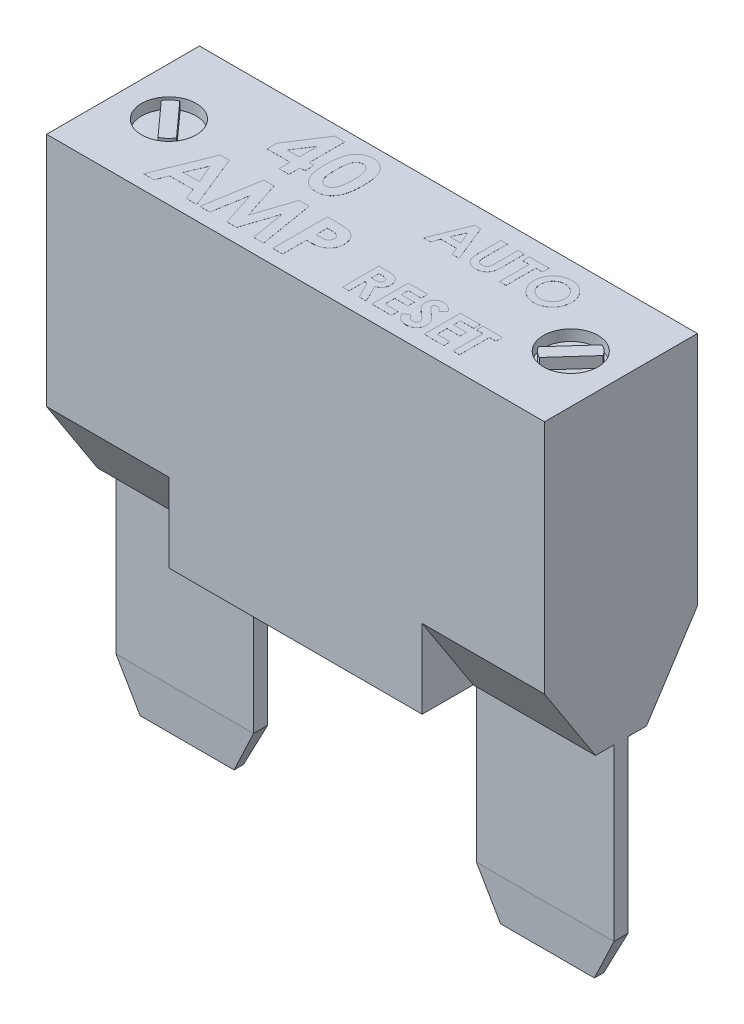
SolidWorks part; units mm, degrees
material "Free-Cutting Brass, UNS C36000"
ref_plane "Front Plane" through (0, 0, 0) normal (0, 0, 1) x (1, 0, 0)
ref_plane "Top Plane" through (0, 0, 0) normal (0, 1, 0) x (1, 0, 0)
ref_plane "Right Plane" through (0, 0, 0) normal (1, 0, 0) x (0, 0, -1)
sketch "Sketch1" plane through (0, 0, 0) normal (1, 0, 0) x (0, 0, -1)
  line L0 (-4.445, 4.572) -> (-1.4816, 0)
  line L1 (-1.4816, 0) -> (1.4816, 0)
  line L2 (0, 0) -> (0, 18.288) construction
  line L6 (1.4816, 0) -> (4.445, 4.572)
  line L7 (4.445, 4.572) -> (4.445, 18.288)
  line L8 (4.445, 18.288) -> (-4.445, 18.288)
  line L9 (-4.445, 18.288) -> (-4.445, 4.572)
  dimension "D1" = 8.89
  dimension "D2" = 18.288
  dimension "D3" = 32.95
  dimension "D4" = 4.572
extrude "Extrude1" add sketch "Sketch1" along normal mid plane 28.956
sketch "Sketch2" plane through (0, 0, 0) normal (1, 0, 0) x (0, 0, -1)
  line L0 (4.445, 18.288) -> (-4.445, 18.288) construction
  line L1 (-4.445, 0) -> (4.445, 0)
  line L2 (-4.445, 0) -> (-4.445, 18.288)
  line L3 (-4.445, 18.288) -> (4.445, 18.288)
  line L4 (4.445, 0) -> (4.445, 18.288)
  line L5 (4.445, 4.572) -> (4.445, 18.288) construction
  line L6 (-1.4816, 0) -> (1.4816, 0) construction
  line L7 (-4.445, 18.288) -> (-4.445, 4.572) construction
extrude "Extrude2" add sketch "Sketch2" along normal mid plane 14.732
sketch "Sketch3" plane through (0, 0, 0) normal (0, -1, 0) x (1, 0, 0)
  line L0 (-14.478, 1.4816) -> (-14.478, -1.4816) construction
  line L1 (-14.478, 0.4064) -> (-6.477, 0.4064)
  line L2 (-14.478, 0.4064) -> (-14.478, -0.4064)
  line L3 (-14.478, -0.4064) -> (-6.477, -0.4064)
  line L4 (-6.477, 0.4064) -> (-6.477, -0.4064)
  line L5 (-14.478, 0.4064) -> (-6.477, -0.4064) construction
  line L6 (-14.478, -0.4064) -> (-6.477, 0.4064) construction
  line L7 (0, 0) -> (-14.478, 0) construction
  point P0 (-10.4775, 0)
  dimension "D1" = 8.001
  dimension "D2" = 0.8128
extrude "Extrude3" add sketch "Sketch3" along normal blind 12.446
chamfer "Chamfer1" distance 2.54 angle 3 2 edges at (-10.4775, -12.446, -0.4064) (-10.4775, -12.446, 0.4064)
chamfer "Chamfer2" distance 2.54 angle 26.57 2 edges at (-14.478, -12.446, 0) (-6.477, -12.446, 0)
sketch "Sketch4" plane through (0, 18.288, 0) normal (0, 1, 0) x (1, 0, 0)
  line L0 (0, 0) -> (0, 7.4677) construction
  line L2 (14.478, -4.445) -> (-14.478, -4.445) construction
  line L3 (-14.478, 4.445) -> (-14.478, -4.445) construction
  circle A0 centre (-11.684, -0.127) radius 1.5875
  circle A1 centre (11.684, -0.127) radius 1.5875
  dimension "D1" = 3.175
  dimension "D2" = 4.318
  dimension "D3" = 2.794
extrude "Extrude4" cut sketch "Sketch4" against normal blind 0.635
sketch "Sketch5" plane through (0, 17.653, 0) normal (0, 1, 0) x (1, 0, 0)
  line L0 (-10.5204, -0.8499) -> (-12.2813, 1.1058)
  line L1 (-12.8476, 0.5959) -> (-11.0867, -1.3598)
  line L2 (-11.684, -0.127) -> (-10.6218, -1.3067) construction
  line L3 (-11.684, -0.127) -> (-10.0965, -0.127) construction
  arc A0 (-11.0867, -1.3598) -> (-10.5204, -0.8499) centre (-11.684, -0.127) ccw
  arc A1 (-12.2813, 1.1058) -> (-12.8476, 0.5959) centre (-11.684, -0.127) ccw
  circle A2 centre (-11.684, -0.127) radius 1.5875 construction
  dimension "D1" = 1.3699
  dimension "D2" = 0.762
  dimension "D3" = 48
extrude "Extrude5" add sketch "Sketch5" along normal up to surface (0.635 mm away) up to face at (11.684, 18.288, -1.4605)
mirror "Mirror1" about plane through (0, 0, 0) normal (1, 0, 0) of "Extrude5", "Extrude3", "Chamfer1", "Chamfer2"
sketch "Sketch7" plane through (0, 18.288, 0) normal (0, 1, 0) x (1, 0, 0)
  line L0 (-14.478, 4.445) -> (-14.478, -4.445) construction
  line L1 (14.478, 4.445) -> (-14.478, 4.445) construction
  text T0 "<b> 40</b>"
  text T1 "<b>AMP</b>"
  text T2 "<b>AUTO</b>\r\n\r\n" font "Century Gothic" height in points 8
  text T3 "<b>RESET</b>" font "Century Gothic" height in points 8
  dimension "D1" = 4.7528
  dimension "D2" = 5.8481
  dimension "D3" = 16.0563
  dimension "D4" = 16.1396
  dimension "D5" = 3.1483
  dimension "D6" = 3.8679
  dimension "D7" = 7.986
  dimension "D8" = 8.0616
extrude "Extrude6" add sketch "Sketch7" along normal blind 0.0025
